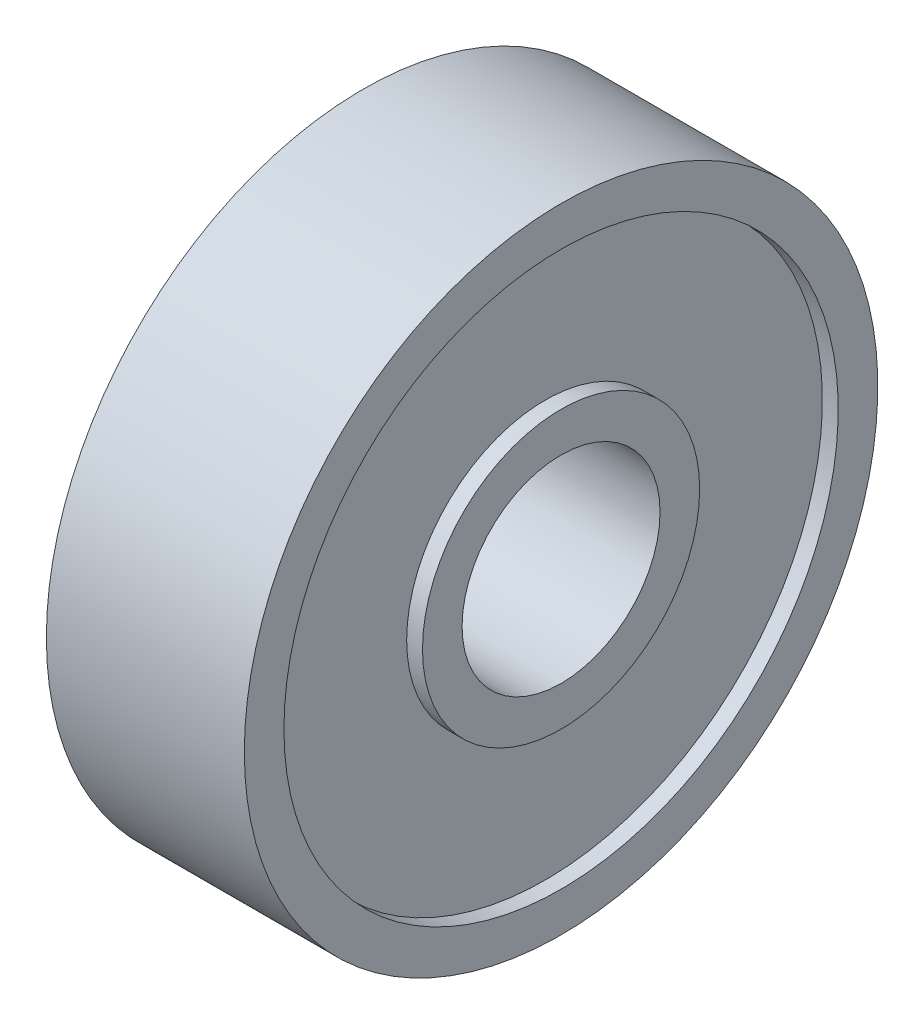
SolidWorks part; units mm, degrees
material "Plain Carbon Steel"
ref_plane "Front Plane" through (0, 0, 0) normal (0, 0, 1) x (1, 0, 0)
ref_plane "Top Plane" through (0, 0, 0) normal (0, 1, 0) x (1, 0, 0)
ref_plane "Right Plane" through (0, 0, 0) normal (1, 0, 0) x (0, 0, -1)
sketch "Sketch1" plane through (0, 0, 0) normal (0, 0, 1) x (1, 0, 0)
  line L0 (-2.5, 0) -> (2.5, 0) construction
  line L1 (-2.5, 8) -> (2.5, 8)
  line L2 (-2.5, 8) -> (-2.5, 7)
  line L3 (-2.5, 2.5) -> (2.5, 2.5)
  line L4 (2.5, 8) -> (2.5, 7)
  line L5 (2.5, 0) -> (2.5, 2.5) construction
  line L6 (-2.5, 0) -> (-2.5, 2.5) construction
  line L7 (0, 0) -> (0, 8) construction
  line L8 (-2.5, 3.5) -> (-2.5, 2.5)
  line L9 (-2.5, 3.5) -> (-2.1, 3.5)
  line L10 (2.5, 3.5) -> (2.5, 2.5)
  line L11 (-2.5, 7) -> (-2.1, 7)
  line L12 (-2.1, 3.5) -> (-2.1, 7)
  line L13 (2.5, 7) -> (2.1, 7)
  line L15 (2.5, 3.5) -> (2.1, 3.5)
  line L16 (2.1, 7) -> (2.1, 3.5)
  dimension "D1" = 16
  dimension "D2" = 5
  dimension "D3" = 5
  dimension "D4" = 0.4
  dimension "D5" = 7
  dimension "D6" = 14
revolve "Revolve1" add sketch "Sketch1" angle 360 about L0
